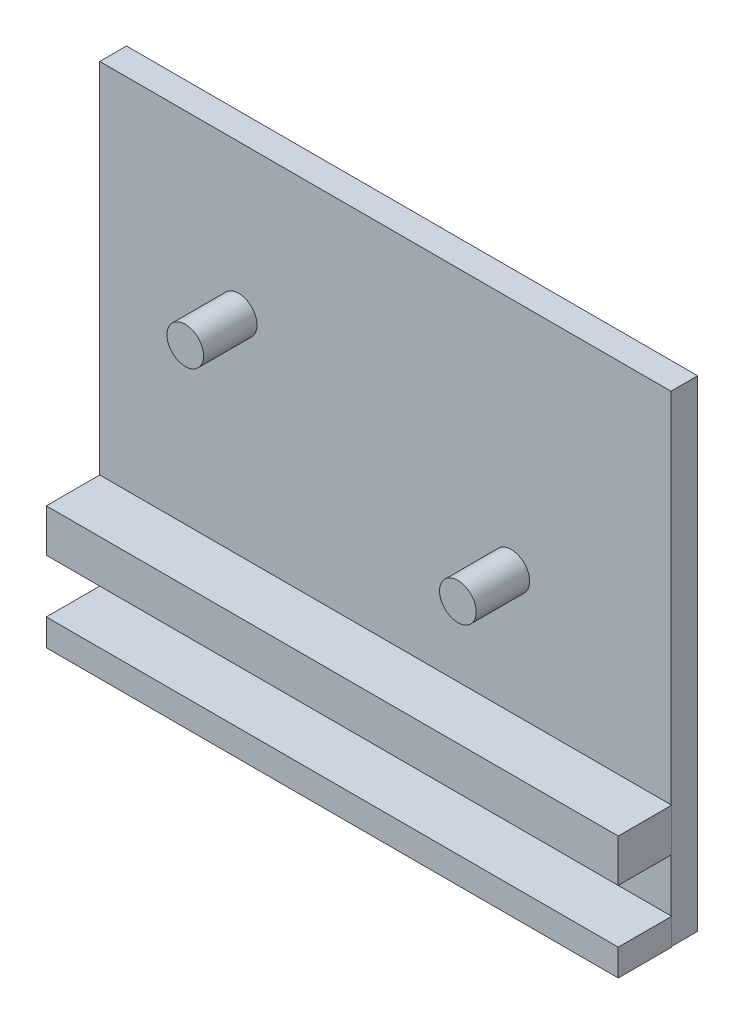
SolidWorks part; units mm, degrees
ref_plane "Front Plane" through (0, 0, 0) normal (0, 0, 1) x (1, 0, 0)
ref_plane "Top Plane" through (0, 0, 0) normal (0, 1, 0) x (1, 0, 0)
ref_plane "Right Plane" through (0, 0, 0) normal (1, 0, 0) x (0, 0, -1)
sketch "Sketch1" plane through (0, 0, 0) normal (0, 0, 1) x (1, 0, 0)
  line L1 (-53.5, 37) -> (53.5, 37)
  line L2 (-53.5, 37) -> (-53.5, -37)
  line L3 (-53.5, -37) -> (53.5, -37)
  line L4 (53.5, 37) -> (53.5, -37)
  line L5 (-53.5, 37) -> (53.5, -37) construction
  line L6 (-53.5, -37) -> (53.5, 37) construction
  circle A0 centre (-27.5, 9) radius 3.4241
  circle A1 centre (23.5, -7) radius 3.4241
  point P0 (0, 0)
  dimension "D1" = 51
  dimension "D2" = 16
  dimension "D3" = 28
  dimension "D4" = 30
  dimension "D5" = 30
  dimension "D6" = 26
extrude "Boss-Extrude1" add sketch "Sketch1" along normal blind 10 contours A0 | A1
sketch "Sketch2" plane through (0, 0, 0) normal (0, 0, -1) x (-1, 0, 0)
  line L1 (-53.3668, 37) -> (53.5, 37)
  line L2 (-53.3668, 37) -> (-53.3668, -53)
  line L3 (-53.3668, -53) -> (53.5, -53)
  line L4 (53.5, 37) -> (53.5, -53)
  line L5 (-53.3668, 37) -> (53.5, -53) construction
  line L6 (-53.3668, -53) -> (53.5, 37) construction
  dimension "D1" = 90
extrude "Boss-Extrude2" add sketch "Sketch2" along normal blind 5
sketch "Sketch3" plane through (0, 0, 0) normal (0, 0, 1) x (1, 0, 0)
  line L0 (53.5, 37) -> (53.5, -37) construction
  line L1 (-53.5, -53) -> (53.5, -53)
  line L2 (-53.5, -53) -> (-53.5, -48)
  line L3 (-53.5, -48) -> (53.5, -48)
  line L4 (53.5, -53) -> (53.5, -48)
  dimension "D1" = 5
extrude "Boss-Extrude3" add sketch "Sketch3" along normal blind 10
sketch "Sketch4" plane through (0, 0, 0) normal (0, 0, 1) x (1, 0, 0)
  line L0 (-53.5, 37) -> (-53.5, -37) construction
  line L1 (-53.5, -30) -> (53.5, -30)
  line L2 (-53.5, -30) -> (-53.5, -38)
  line L3 (-53.5, -38) -> (53.5, -38)
  line L4 (53.5, -30) -> (53.5, -38)
  line L5 (53.5, 37) -> (53.5, -37) construction
  line L6 (53.5, -48) -> (-53.5, -48) construction
  dimension "D1" = 10
  dimension "D2" = 8
extrude "Boss-Extrude4" add sketch "Sketch4" along normal blind 10
